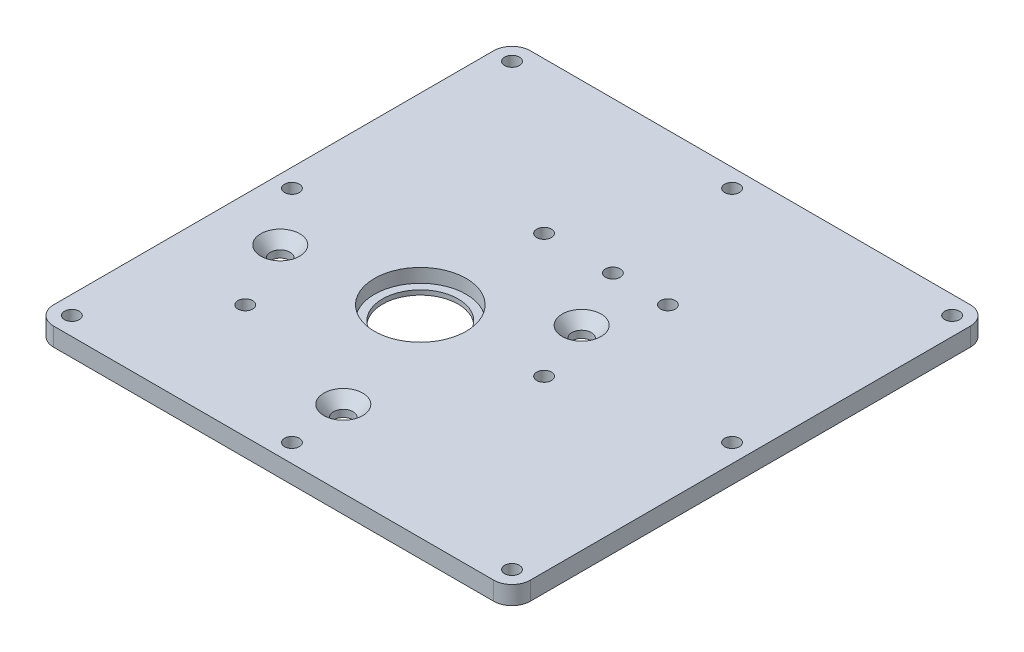
SolidWorks part; units mm, degrees
material "5052-H32"
ref_plane "Front Plane" through (0, 0, 0) normal (0, 0, 1) x (1, 0, 0)
ref_plane "Top Plane" through (0, 0, 0) normal (0, 1, 0) x (1, 0, 0)
ref_plane "Right Plane" through (0, 0, 0) normal (1, 0, 0) x (0, 0, -1)
sketch "Sketch1" plane through (0, 0, 0) normal (0, 1, 0) x (1, 0, 0)
  line L1 (82.55, -82.55) -> (-82.55, -82.55)
  line L2 (82.55, -82.55) -> (82.55, 82.55)
  line L3 (82.55, 82.55) -> (-82.55, 82.55)
  line L4 (-82.55, -82.55) -> (-82.55, 82.55)
  line L5 (82.55, -82.55) -> (-82.55, 82.55) construction
  line L6 (82.55, 82.55) -> (-82.55, -82.55) construction
  circle A0 centre (-19.05, -12.7) radius 13.0969
  circle A1 centre (23.8125, -12.7) radius 1.5875
  point P0 (0, 0)
  dimension "D5" = 26.1937
  dimension "D6" = 3.175
  dimension "D1" = 165.1
  dimension "D2" = 165.1
  dimension "D3" = 42.8625
  dimension "D4" = 63.5
  dimension "D7" = 69.85
extrude "Boss-Extrude1" add sketch "Sketch1" along normal blind 6.35
sketch "Sketch3" plane through (0, 6.35, 0) normal (0, -1, 0) x (1, 0, 0)
  circle A0 centre (-19.05, 12.7) radius 15.875
  dimension "D1" = 31.75
extrude "Cut-Extrude1" cut sketch "Sketch3" along normal blind 4.7625
sketch "Sketch6" plane through (0, 6.35, 0) normal (0, 1, 0) x (1, 0, 0)
  circle A0 centre (-2.54, -55.8793) radius 3.175
  circle A1 centre (-61.2558, -18.9906) radius 3.175
  circle A2 centre (15.0154, 9.1011) radius 3.175
  circle A5 centre (-19.05, -12.7) radius 15.875 construction
  circle A6 centre (-19.05, -12.7) radius 15.875
  dimension "D3" = 6.35
  dimension "D1" = 16.51
  dimension "D2" = 46.228
  dimension "D4" = 42.672
  dimension "D5" = 69.342
  dimension "D6" = 81.28
  dimension "D7" = 67.31
hole_wizard "CSK for 1/4 Flat Head Socket Cap Screw1" positions "Sketch7" profile "Sketch8" countersink size "1/4" standard "ANSI Inch" end condition through all
sketch "Sketch7" plane through (0, 6.35, 0) normal (0, 1, 0) x (1, 0, 0)
  point P0 (-61.2558, -18.9906)
  point P3 (15.0154, 9.1011)
  point P6 (-2.54, -55.8793)
sketch "Sketch8" plane through (-61.2558, 6.35, 18.9906) normal (1, 0, 0) x (0, 0, 1)
  line L0 (0, 0) -> (0, 6.35)
  line L1 (0, 6.35) -> (3.3782, 6.35)
  line L2 (3.3782, 6.35) -> (3.3782, 3.8716)
  line L3 (3.3782, 3.8716) -> (6.7437, 0)
  line L5 (6.7437, 0) -> (0, 0)
  line L6 (-3.3782, 3.8716) -> (-6.7437, 0) construction
  line L11 (0, -6.35) -> (0, 107.95) construction
  dimension "Thru Hole Dia." = 6.7564
  dimension "Thru Hole Depth" = 6.35
  dimension "Near C'Sink Dia." = 13.4874
  dimension "Near C'Sink Angle" = 82
fillet "Fillet1" radius 6.35 4 edges at (82.55, 3.175, -82.55) (82.55, 3.175, 82.55) (-82.55, 3.175, 82.55) (-82.55, 3.175, -82.55)
hole_wizard "#10 Clearance Hole1" positions "Sketch9" profile "Sketch10" hole size "#10" standard "ANSI Inch" end condition through all
sketch "Sketch9" plane through (0, 6.35, 0) normal (0, 1, 0) x (1, 0, 0)
  line L0 (-76.2, 76.2) -> (76.2, 76.2)
  line L1 (76.2, 76.2) -> (76.2, -76.2)
  line L2 (76.2, -76.2) -> (-76.2, -76.2)
  line L3 (-76.2, -76.2) -> (-76.2, 76.2)
  point P0 (-76.2, -76.2)
  point P3 (-76.2, 76.2)
  point P6 (76.2, 76.2)
  point P9 (76.2, -76.2)
  point P21 (0, 76.2)
  point P23 (0, -76.2)
  point P32 (-76.2, 0)
  point P36 (76.2, 0)
sketch "Sketch10" plane through (-76.2, 6.35, 76.2) normal (1, 0, 0) x (0, 0, 1)
  line L0 (0, 0) -> (0, 6.35)
  line L1 (0, 6.35) -> (2.5527, 6.35)
  line L2 (2.5527, 6.35) -> (2.5527, 0)
  line L5 (2.5527, 0) -> (0, 0)
  line L11 (0, -6.35) -> (0, 107.95) construction
  dimension "Thru Hole Dia." = 5.1054
  dimension "Thru Hole Depth" = 6.35
hole_wizard "1/4-20 Tapped Hole1" positions "Sketch11" profile "Sketch13" tap size "1/4-20" standard "ANSI Inch"
sketch "Sketch11" plane through (0, 6.35, 0) normal (0, 1, 0) x (1, 0, 0)
  circle A1 centre (-19.05, -12.7) radius 13.0969 construction
  circle A2 centre (-19.05, -12.7) radius 42.8625 construction
  point P0 (23.8125, -12.7)
  point P12 (-49.3584, -43.0084)
  point P13 (-19.05, 30.1625)
  point P14 (-19.05, -12.7)
  dimension "D1" = 90
  dimension "D2" = 135
sketch "Sketch13" plane through (23.8125, 6.35, 12.7) normal (1, 0, 0) x (0, 0, 1)
  line L0 (0, 0) -> (0, 17.5358)
  line L1 (0, 17.5358) -> (2.5527, 16.002)
  line L2 (2.5527, 16.002) -> (2.5527, 0)
  line L5 (2.5527, 0) -> (0, 0)
  line L10 (0, 17.5358) -> (-2.5527, 16.002) construction
  line L11 (0, -6.35) -> (0, 107.95) construction
  dimension "Tap Drill Dia." = 5.1054
  dimension "Tap Drill Depth" = 16.002
  dimension "Drill Angle" = 118
hole_wizard "#10 Clearance Hole2" positions "Sketch14" profile "Sketch15" hole size "#10" standard "ANSI Inch" end condition through all
sketch "Sketch14" plane through (0, 6.35, 0) normal (0, 1, 0) x (1, 0, 0)
  line L0 (23.8125, -12.7) -> (23.8125, 30.1625) construction
  line L1 (23.8125, 30.1625) -> (-19.05, 30.1625) construction
  point P0 (23.8125, 30.1625)
  point P17 (4.7625, 30.1625)
  dimension "D4" = 19.05
sketch "Sketch15" plane through (23.8125, 6.35, -30.1625) normal (1, 0, 0) x (0, 0, 1)
  line L0 (0, 0) -> (0, 6.35)
  line L1 (0, 6.35) -> (2.5527, 6.35)
  line L2 (2.5527, 6.35) -> (2.5527, 0)
  line L5 (2.5527, 0) -> (0, 0)
  line L11 (0, -6.35) -> (0, 107.95) construction
  dimension "Thru Hole Dia." = 5.1054
  dimension "Thru Hole Depth" = 6.35
sketch "Sketch16" plane through (0, 0, 0) normal (0, -1, 0) x (1, 0, 0)
  line L0 (-76.2, 82.55) -> (76.2, 82.55) construction
  line L1 (69.85, -69.85) -> (-69.85, -69.85)
  line L2 (69.85, -69.85) -> (69.85, 69.85)
  line L3 (69.85, 69.85) -> (-69.85, 69.85)
  line L4 (-69.85, -69.85) -> (-69.85, 14.4324)
  line L5 (69.85, -69.85) -> (-69.85, 69.85) construction
  line L6 (69.85, 69.85) -> (-69.85, -69.85) construction
  line L7 (82.55, 76.2) -> (82.55, -76.2) construction
  line L8 (-69.85, 23.5488) -> (-69.85, 69.85)
  circle A0 centre (-19.05, 12.7) radius 13.0969 construction
  circle A1 centre (-61.2558, 18.9906) radius 3.3782 construction
  circle A2 centre (-49.3584, 43.0084) radius 2.5527 construction
  circle A3 centre (-19.05, -30.1625) radius 2.5527 construction
  circle A4 centre (-2.54, 55.8793) radius 3.3782 construction
  circle A5 centre (23.8125, 12.7) radius 2.5527 construction
  circle A6 centre (15.0154, -9.1011) radius 3.3782 construction
  circle A7 centre (4.7625, -30.1625) radius 2.5527 construction
  circle A8 centre (-49.3584, 43.0084) radius 2.5527
  circle A9 centre (23.8125, -30.1625) radius 2.5527 construction
  circle A10 centre (-19.05, -30.1625) radius 2.5527
  circle A11 centre (-19.05, 12.7) radius 13.0969
  circle A12 centre (-61.2558, 18.9906) radius 3.3782
  circle A15 centre (-2.54, 55.8793) radius 3.3782
  circle A16 centre (23.8125, 12.7) radius 2.5527
  circle A17 centre (15.0154, -9.1011) radius 3.3782
  circle A18 centre (4.7625, -30.1625) radius 2.5527
  circle A20 centre (23.8125, -30.1625) radius 2.5527
  circle A22 centre (-19.05, 12.7) radius 19.4469
  arc A23 (-69.85, 14.4324) -> (-69.85, 23.5488) centre (-61.2558, 18.9906) ccw
  circle A26 centre (-2.54, 55.8793) radius 9.7282
  arc A27 (24.1266, 3.8028) -> (16.5225, 7.5898) centre (23.8125, 12.7) ccw
  arc A28 (23.203, -14.3548) -> (21.7783, -2.1081) centre (15.0154, -9.1011) ccw
  arc A29 (3.3883, -21.3665) -> (10.9679, -36.5461) centre (4.7625, -30.1625) ccw
  arc A31 (17.6071, -36.5461) -> (26.0268, -21.5396) centre (23.8125, -30.1625) ccw
  circle A33 centre (-19.05, -30.1625) radius 8.9027
  circle A34 centre (-61.2558, 18.9906) radius 9.7282 construction
  arc A36 (3.3883, -21.3665) -> (6.7161, -14.1764) centre (2.6531, -16.6611) ccw
  arc A37 (23.203, -14.3548) -> (26.0268, -21.5396) centre (27.2113, -16.9267) ccw
  arc A38 (17.6071, -36.5461) -> (10.9679, -36.5461) centre (14.2875, -39.9611) ccw
  arc A39 (23.5092, -4.3584) -> (26.7018, 4.2792) centre (26.2471, -0.4615) cw
  circle A40 centre (4.7625, -30.1625) radius 8.9027 construction
  circle A41 centre (15.0154, -9.1011) radius 9.7282 construction
  circle A42 centre (23.8125, -30.1625) radius 8.9027 construction
  arc A43 (13.0908, 0.4348) -> (16.5225, 7.5898) centre (12.4315, 5.1515) ccw
  circle A44 centre (23.8125, 12.7) radius 8.9027 construction
  arc A45 (13.47, 0.5036) -> (6.7161, -14.1764) centre (15.0154, -9.1011) ccw
  circle A46 centre (-49.3584, 43.0084) radius 7.333
  point P4 (0, 0)
  point P25 (-45.6027, 21.8349)
  point P46 (38.3847, -21.9062)
  point P63 (19.3347, -21.9062)
  point P67 (30.6685, -6.2568)
  dimension "D5" = 4.7625
  dimension "D6" = 4.7625
  dimension "D7" = 4.7625
  dimension "D2" = 12.7
  dimension "D3" = 12.7
  dimension "D1" = 6.35
  dimension "D4" = 6.35
extrude "Cut-Extrude2" cut sketch "Sketch16" against normal blind 3.175 contours A23 L4 L1 L2 L3 L8 A31 A29 A28 A27 A26 A22
fillet "Fillet2" radius 3.175 6 edges at (69.85, 1.5875, 69.85) (-69.85, 1.5875, 69.85) (-69.85, 1.5875, 14.4324) (-69.85, 1.5875, 23.5488) (-69.85, 1.5875, -69.85) (69.85, 1.5875, -69.85)
equation "\"D3@Sketch1\"=2.5/2+.625/2+.125"
equation "\"D4@Sketch16\"=\"D1@Sketch16\""
